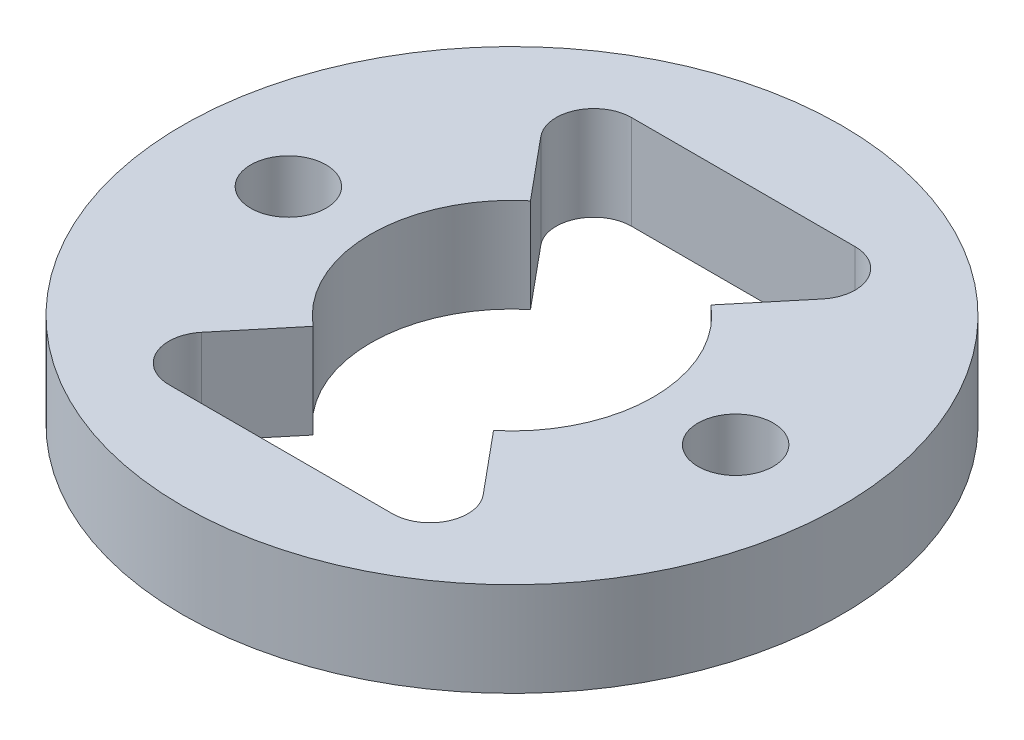
SolidWorks part; units mm, degrees
ref_plane "Front Plane" through (0, 0, 0) normal (0, 0, 1) x (1, 0, 0)
ref_plane "Top Plane" through (0, 0, 0) normal (0, 1, 0) x (1, 0, 0)
ref_plane "Right Plane" through (0, 0, 0) normal (1, 0, 0) x (0, 0, -1)
sketch "Sketch1" plane through (0, 7.1687, 0) normal (0, -1, 0) x (1, 0, 0)
  circle A0 centre (7.1147, 17.6253) radius 14
  arc A1 (16.9407, 19.1918) -> (13.3843, 25.3516) centre (7.1147, 17.6253) ccw construction
  circle A2 centre (7.1147, 17.6253) radius 6
  circle A3 centre (2.3647, 25.8526) radius 1.6
  circle A4 centre (-2.3853, 17.6253) radius 1.6
  circle A5 centre (2.3647, 9.3981) radius 1.6
  circle A6 centre (11.8647, 9.3981) radius 1.6
  circle A7 centre (16.6147, 17.6253) radius 1.6
  circle A8 centre (11.8647, 25.8526) radius 1.6
  arc A9 (0.8452, 25.3516) -> (3.5584, 26.9181) centre (2.3647, 25.8526) ccw construction
  arc A10 (-2.7112, 16.0589) -> (-2.7112, 19.1918) centre (-2.3853, 17.6253) ccw construction
  arc A11 (3.5584, 8.3326) -> (0.8452, 9.8991) centre (2.3647, 9.3981) ccw construction
  arc A12 (13.3843, 9.8991) -> (10.6711, 8.3326) centre (11.8647, 9.3981) ccw construction
  arc A13 (16.9407, 19.1918) -> (16.9407, 16.0589) centre (16.6147, 17.6253) ccw construction
  arc A14 (10.6711, 26.9181) -> (13.3843, 25.3516) centre (11.8647, 25.8526) ccw construction
  dimension "D1" = 28
  dimension "D2" = 12
extrude "Boss-Extrude1" add sketch "Sketch1" along normal blind 4
sketch "Sketch2" plane through (0, 3.1687, 0) normal (0, -1, 0) x (1, 0, 0)
  line L0 (11.8647, 7.7981) -> (2.3647, 7.7981)
  line L1 (13.0959, 10.42) -> (7.1147, 17.6253) construction
  line L2 (7.1147, 17.6253) -> (1.1336, 10.42) construction
  line L3 (11.8647, 7.7981) -> (13.0959, 10.42)
  line L4 (2.3647, 7.7981) -> (1.1336, 10.42)
  line L5 (7.1147, 17.6253) -> (13.0959, 24.8306) construction
  line L6 (7.1147, 17.6253) -> (1.1336, 24.8306) construction
  line L7 (13.0959, 10.42) -> (10.947, 13.0087)
  line L8 (10.947, 13.0087) -> (3.2825, 13.0087)
  line L9 (3.2825, 13.0087) -> (1.1336, 10.42)
  line L10 (1.1336, 24.8306) -> (2.3647, 27.4526)
  line L11 (2.3647, 27.4526) -> (11.8647, 27.4526)
  line L12 (11.8647, 27.4526) -> (13.0959, 24.8306)
  line L13 (13.0959, 24.8306) -> (10.947, 22.242)
  line L14 (10.947, 22.242) -> (3.2825, 22.242)
  line L15 (3.2825, 22.242) -> (1.1336, 24.8306)
  circle A0 centre (11.8647, 25.8526) radius 1.6 construction
  circle A1 centre (2.3647, 25.8526) radius 1.6 construction
  circle A2 centre (11.8647, 9.3981) radius 1.6 construction
  circle A3 centre (2.3647, 9.3981) radius 1.6 construction
  circle A4 centre (7.1147, 17.6253) radius 6 construction
extrude "Cut-Extrude1" cut sketch "Sketch2" against normal up to next
